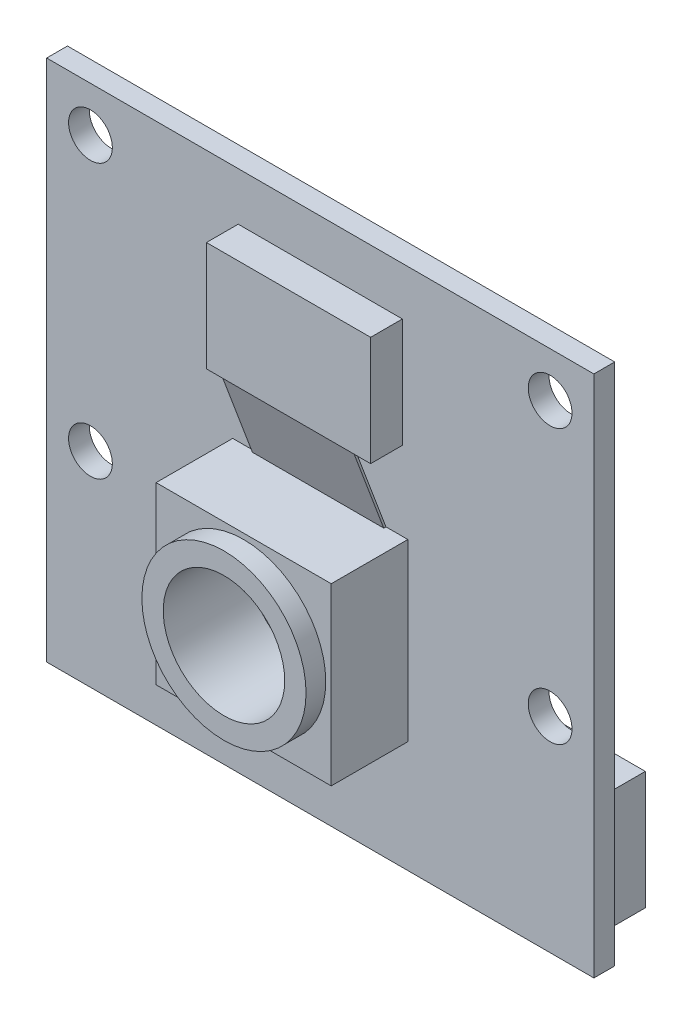
SolidWorks part; units mm, degrees
material "Silicon"
ref_plane "Front Plane" through (0, 0, 0) normal (0, 0, 1) x (1, 0, 0)
ref_plane "Top Plane" through (0, 0, 0) normal (0, 1, 0) x (1, 0, 0)
ref_plane "Right Plane" through (0, 0, 0) normal (1, 0, 0) x (0, 0, -1)
sketch "Sketch1" plane through (0, 0, 0) normal (0, 0, 1) x (1, 0, 0)
  line L1 (0, 0) -> (25, 0)
  line L2 (0, 0) -> (0, 23.9)
  line L3 (0, 23.9) -> (25, 23.9)
  line L4 (25, 0) -> (25, 23.9)
  circle A0 centre (2, 21.85) radius 1
  circle A1 centre (23, 21.85) radius 1
  circle A2 centre (2, 9.35) radius 1
  circle A3 centre (23, 9.35) radius 1
  dimension "D3" = 2
  dimension "D4" = 21
  dimension "D5" = 2
  dimension "D6" = 21
  dimension "D7" = 2
  dimension "D8" = 12.5
  dimension "D9" = 2.05
  dimension "D1" = 25
  dimension "D2" = 23.9
extrude "Boss-Extrude1" add sketch "Sketch1" along normal blind 0.95 contours L1 L4 L3 L2 A3 A2 A1 A0
sketch "Sketch2" plane through (0, 0, 0.95) normal (0, 0, 1) x (1, 0, 0)
  line L0 (25, 0) -> (25, 23.9) construction
  line L1 (8.75, 21.7) -> (16.25, 21.7)
  line L2 (8.75, 21.7) -> (8.75, 16.7)
  line L3 (8.75, 16.7) -> (16.25, 16.7)
  line L4 (16.25, 21.7) -> (16.25, 16.7)
  line L5 (0, 0) -> (25, 0) construction
  dimension "D1" = 7.5
  dimension "D2" = 5
  dimension "D3" = 8.75
  dimension "D4" = 16.7
extrude "Boss-Extrude2" add sketch "Sketch2" along normal blind 1.45
sketch "Sketch3" plane through (0, 0, 0.95) normal (0, 0, 1) x (1, 0, 0)
  line L0 (25, 0) -> (25, 23.9) construction
  line L1 (8.5, 13.1) -> (16.5, 13.1)
  line L2 (8.5, 13.1) -> (8.5, 5.1)
  line L3 (8.5, 5.1) -> (16.5, 5.1)
  line L4 (16.5, 13.1) -> (16.5, 5.1)
  line L5 (0, 0) -> (25, 0) construction
  circle A0 centre (23, 9.35) radius 1 construction
  dimension "D1" = 8
  dimension "D2" = 8
  dimension "D3" = 8.5
  dimension "D4" = 5.1
  dimension "D5" = 3.75
extrude "Boss-Extrude3" add sketch "Sketch3" along normal blind 4.4
sketch "Sketch4" plane through (0, 0, 5.35) normal (0, 0, 1) x (1, 0, 0)
  circle A0 centre (12.5, 9.1) radius 3.75
  line M2 (8.5, 13.1) -> (8.5, 5.1)
  line M3 (8.5, 5.1) -> (16.5, 5.1)
  line M4 (16.5, 5.1) -> (16.5, 13.1)
  line M5 (16.5, 13.1) -> (8.5, 13.1)
extrude "Cut-Extrude1" cut sketch "Sketch4" against normal blind 0.9 contours A0 M5 M2 M3 M4
sketch "Sketch5" plane through (0, 0, 5.35) normal (0, 0, 1) x (1, 0, 0)
  circle A0 centre (12.5, 9.1) radius 2.775
  dimension "D1" = 5.55
extrude "Cut-Extrude2" cut sketch "Sketch5" against normal blind 3.9
ref_plane "Plane3" through (15.5, 0, 0) normal (1, 0, 0) x (0, 0, -1)
ref_plane "Plane4" through (9.5, 0, 0) normal (-1, 0, 0) x (0, 0, 1)
sketch "Sketch12" plane through (15.5, 0, 0) normal (1, 0, 0) x (0, 0, -1)
  line L0 (-2.4, 16.7) -> (-2.3, 16.7)
  line L1 (-2.4, 16.7) -> (-0.95, 16.7) construction
  line L2 (-2.3, 16.7) -> (-0.95, 13.1)
  line L3 (-0.95, 0) -> (-0.95, 23.9) construction
  line L4 (-4.45, 13.1) -> (-0.95, 13.1) construction
  line L5 (-0.95, 13.1) -> (-1.05, 13.1)
  line L6 (-2.4, 16.7) -> (-1.05, 13.1)
  dimension "D1" = 0.1
  dimension "D2" = 0.1
extrude "Boss-Extrude4" add sketch "Sketch12" against normal up to surface (6 mm away) up to plane "Plane4"
sketch "Sketch13" plane through (0, 0, 0) normal (0, 0, -1) x (-1, 0, 0)
  line L0 (-12.5, 0.2) -> (-12.5, 5.6)
  line L2 (0, 5.6) -> (-1.4, 5.6)
  line L3 (0, 0) -> (0, 23.9) construction
  line L4 (-1.4, 5.6) -> (-12.5, 5.6)
  line L5 (-12.5, 5.6) -> (-23.6, 5.6)
  line L6 (-23.6, 5.6) -> (-23.6, 0.2)
  line L7 (-1.4, 5.6) -> (-1.4, 0.2)
  line L9 (-23.6, 0.2) -> (-1.4, 0.2)
  line M5 (-25, 0) -> (0, 0)
  dimension "D2" = 1.4
  dimension "D3" = 11.1
extrude "Boss-Extrude5" add sketch "Sketch13" along normal blind 2.8 contours L5 L6 L0 M5 | L7 L4 L0 M5
